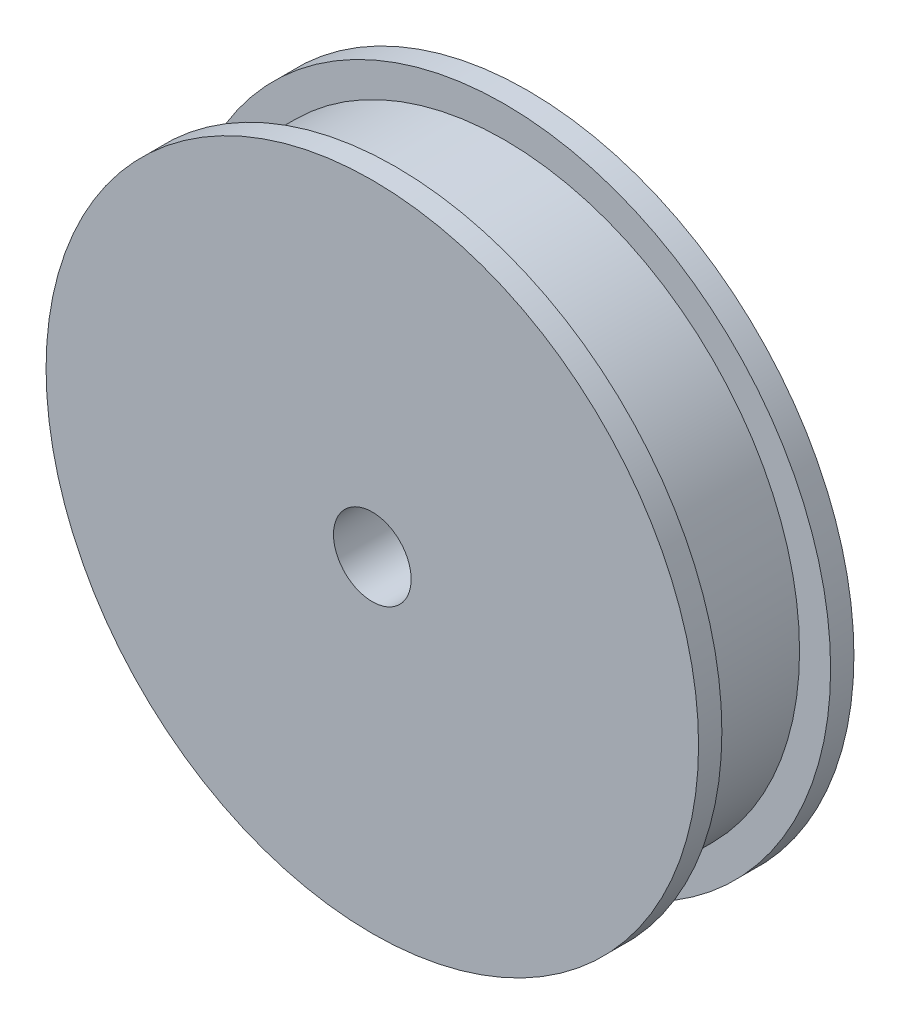
SolidWorks part; units mm, degrees
ref_plane "Спереди" through (0, 0, 0) normal (0, 0, 1) x (1, 0, 0)
ref_plane "Сверху" through (0, 0, 0) normal (0, 1, 0) x (1, 0, 0)
ref_plane "Справа" through (0, 0, 0) normal (1, 0, 0) x (0, 0, -1)
sketch "Эскиз2" plane through (0, 0, 0) normal (1, 0, 0) x (0, 0, -1)
  line L0 (0, 0) -> (0, 21)
  line L1 (0, 21) -> (1.5, 21)
  line L2 (1.5, 21) -> (1.5, 19)
  line L3 (1.5, 19) -> (8.5, 19)
  line L4 (8.5, 19) -> (8.5, 21)
  line L5 (8.5, 21) -> (10, 21)
  line L6 (10, 21) -> (10, 0)
  line L7 (10, 0) -> (0, 0)
  line L8 (5, 0) -> (5, 19) construction
  dimension "D1" = 21
  dimension "D2" = 19
  dimension "D3" = 10
  dimension "D4" = 7
revolve "Повернуть1" add sketch "Эскиз2" angle 360 about L7
sketch "Эскиз3" plane through (0, 0, -10) normal (0, 0, -1) x (-1, 0, 0)
  circle A0 centre (0, 0) radius 10
  dimension "D1" = 20
extrude "Бобышка-Вытянуть1" add sketch "Эскиз3" along normal blind 7
sketch "Эскиз4" plane through (0, 0, -17) normal (0, 0, -1) x (-1, 0, 0)
  circle A0 centre (0, 0) radius 2.5
  dimension "D1" = 5
extrude "Вырез-Вытянуть1" cut sketch "Эскиз4" against normal through all
sketch "Эскиз5" plane through (0, 0, 0) normal (0, 0, 1) x (1, 0, 0)
  line L0 (0, 0) -> (19, 0) construction
  circle A0 centre (0, 0) radius 19 construction
  circle A1 centre (0, 0) radius 19 construction
ref_plane "Плоскость1" through (19, 0, 0) normal (1, 0, 0) x (0, 0, -1)
